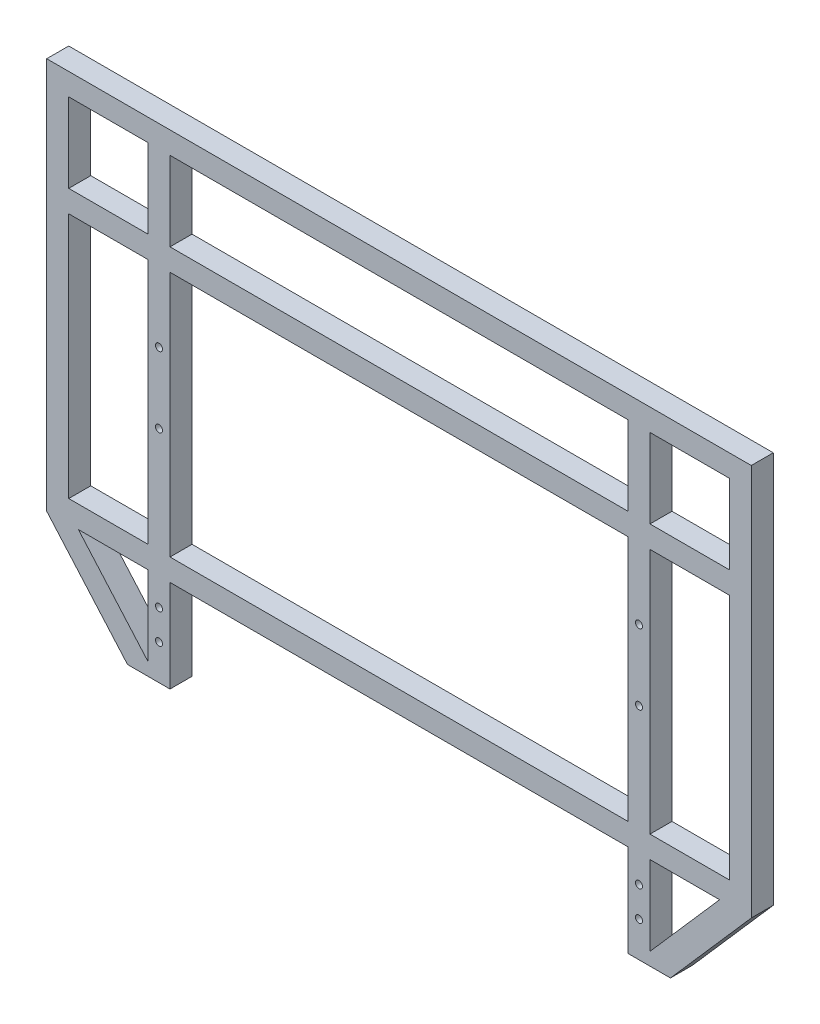
SolidWorks part; units mm, degrees
ref_plane "Front Plane" through (0, 0, 0) normal (0, 0, 1) x (1, 0, 0)
ref_plane "Top Plane" through (0, 0, 0) normal (0, 1, 0) x (1, 0, 0)
ref_plane "Right Plane" through (0, 0, 0) normal (1, 0, 0) x (0, 0, -1)
sketch "Sketch1" plane through (0, 0, 0) normal (0, 0, 1) x (1, 0, 0)
  line L0 (0, 0) -> (0, -332.3241) construction
  line L1 (0, 0) -> (-200, 0)
  line L2 (-200, 0) -> (-200, -222.5)
  line L3 (-200, -222.5) -> (-130, -302.5)
  line L4 (-187.5, -12.5) -> (-187.5, -57.5)
  line L5 (-182.0103, -222.5) -> (-142.5, -267.6546)
  line L6 (-142.5, -267.6546) -> (-142.5, -222.5)
  line L7 (130, -70) -> (-130, -70)
  line L8 (130, -210) -> (-130, -210)
  line L9 (130, -12.5) -> (-130, -12.5)
  line L10 (-187.5, -57.5) -> (-142.5, -57.5)
  line L11 (-187.5, -70) -> (-187.5, -210)
  line L12 (-182.0103, -222.5) -> (-142.5, -222.5)
  line L13 (0, -70) -> (-200, -70) construction
  line L14 (-142.5, -210) -> (-142.5, -70)
  line L15 (0, -210) -> (-200, -210) construction
  line L16 (-130, -302.5) -> (-130, -222.5)
  line L17 (-130, -210) -> (-130, -70)
  line L18 (-142.5, -210) -> (-187.5, -210)
  line L19 (-130, -222.5) -> (130, -222.5)
  line L20 (-142.5, -12.5) -> (-187.5, -12.5)
  line L21 (-130, -57.5) -> (130, -57.5)
  line L22 (-142.5, -57.5) -> (-142.5, -12.5)
  line L23 (-130, -57.5) -> (-130, -12.5)
  line L24 (-142.5, -70) -> (-187.5, -70)
  line L25 (142.5, -70) -> (187.5, -70)
  line L26 (130, -57.5) -> (130, -12.5)
  line L27 (142.5, -57.5) -> (142.5, -12.5)
  line L28 (142.5, -12.5) -> (187.5, -12.5)
  line L29 (142.5, -210) -> (187.5, -210)
  line L30 (130, -210) -> (130, -70)
  line L31 (130, -302.5) -> (130, -222.5)
  line L32 (142.5, -210) -> (142.5, -70)
  line L33 (182.0103, -222.5) -> (142.5, -222.5)
  line L34 (187.5, -70) -> (187.5, -210)
  line L35 (187.5, -57.5) -> (142.5, -57.5)
  line L36 (142.5, -267.6546) -> (142.5, -222.5)
  line L37 (182.0103, -222.5) -> (142.5, -267.6546)
  line L38 (187.5, -12.5) -> (187.5, -57.5)
  line L39 (200, -222.5) -> (130, -302.5)
  line L40 (200, 0) -> (200, -222.5)
  line L41 (0, 0) -> (200, 0)
  line L42 (-154.1261, -274.9273) -> (-130, -274.9273)
  line L43 (130, -274.9273) -> (154.1261, -274.9273)
  point P40 (0, -57.5)
  point P42 (0, -222.5)
  point P50 (0, -12.5)
  dimension "D1" = 70
  dimension "150" = 200
  dimension "D3" = 12.5
  dimension "D4" = 12.5
  dimension "D5" = 12.5
  dimension "D6" = 12.5
  dimension "D7" = 45
  dimension "D8" = 130
  dimension "D9" = 60
  dimension "D10" = 80
  dimension "D12" = 7.2727
  dimension "D2" = 140
extrude "Boss-Extrude1" add sketch "Sketch1" along normal blind 12.5
sketch "Sketch2" plane through (0, 0, 0) normal (0, 0, -1) x (-1, 0, 0)
  line L0 (183.3601, -130) -> (-183.3601, -130) construction
  line L1 (200, 0) -> (-200, 0) construction
  line L2 (142.5, -210) -> (142.5, -70) construction
  line L3 (0, -130) -> (0, 0) construction
  circle A0 centre (136.25, -110) radius 2
  circle A1 centre (136.25, -150) radius 2
  circle A2 centre (-136.25, -110) radius 2
  circle A3 centre (-136.25, -150) radius 2
  point P3 (0, -130)
  dimension "D2" = 4
  dimension "D1" = 130
  dimension "D3" = 6.25
  dimension "D4" = 20
extrude "Cut-Extrude1" cut sketch "Sketch2" against normal blind 15
sketch "Sketch3" plane through (0, 0, 12.5) normal (0, 0, 1) x (1, 0, 0)
  line L0 (-130, -274.9273) -> (-130, -222.5) construction
  line L1 (-154.1261, -274.9273) -> (-130, -274.9273) construction
  line L2 (0, 0) -> (0, -246.5328) construction
  line L3 (-200, 0) -> (200, 0) construction
  circle A0 centre (-136.25, -237.9273) radius 2
  circle A1 centre (-136.25, -254.9273) radius 2
  circle A2 centre (136.25, -254.9273) radius 2
  circle A3 centre (136.25, -237.9273) radius 2
  dimension "D2" = 4
  dimension "D3" = 4
  dimension "D1" = 6.25
  dimension "D4" = 17
  dimension "D5" = 20
extrude "Cut-Extrude2" cut sketch "Sketch3" against normal blind 15
